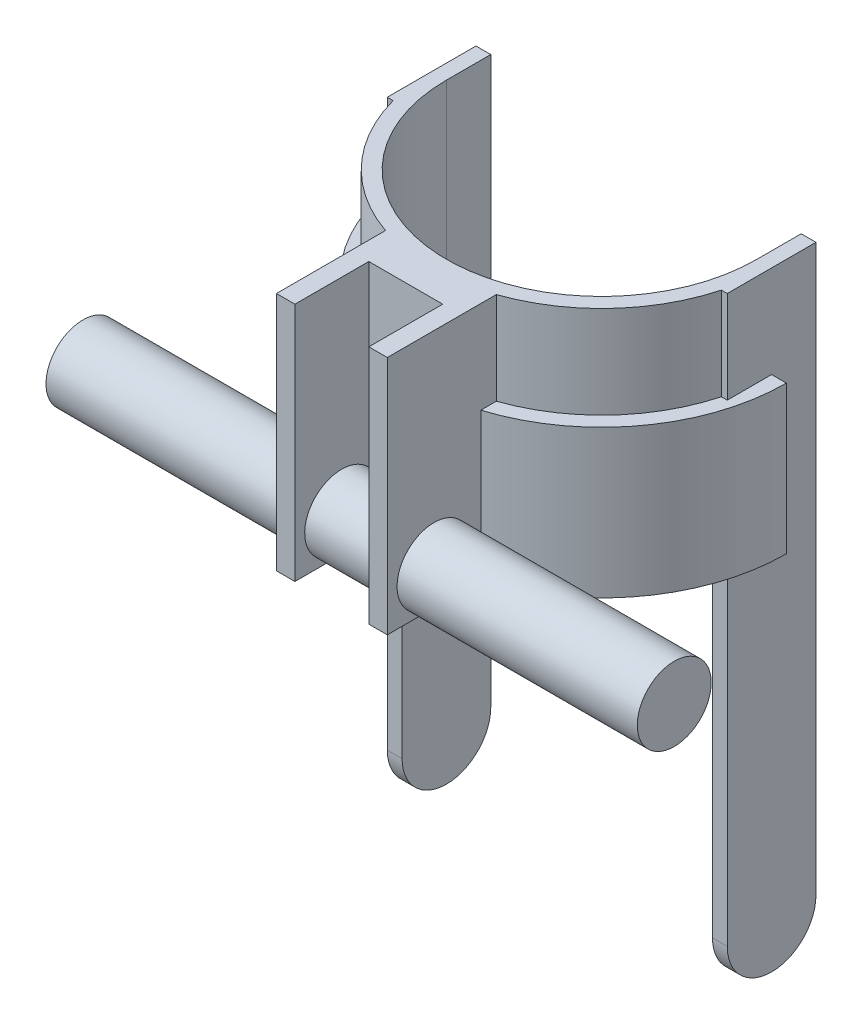
SolidWorks part; units mm, degrees
ref_plane "Front" through (0, 0, 0) normal (0, 0, 1) x (1, 0, 0)
ref_plane "Top" through (0, 0, 0) normal (0, 1, 0) x (1, 0, 0)
ref_plane "Right" through (0, 0, 0) normal (1, 0, 0) x (0, 0, -1)
sketch "草图1" plane through (0, 0, 0) normal (0, 1, 0) x (1, 0, 0)
  line L0 (-42, 0) -> (0, 0) construction
  line L1 (-46, 0) -> (-84.254, 0) construction
  line L2 (0, 0) -> (0, 41.4) construction
  line L5 (-46, 0) -> (-46, 12)
  line L6 (-46, 12) -> (-42, 12)
  line L7 (-42, 0) -> (-42, 12)
  line L11 (46, 0) -> (46, 12)
  line L12 (46, 12) -> (42, 12)
  line L13 (42, 0) -> (42, 12)
  line L14 (0, -42) -> (43.7489, -42) construction
  line L16 (-15, -43.4856) -> (-15, -73)
  line L17 (-15, -73) -> (-10, -73)
  line L18 (15, -43.4856) -> (15, -73)
  line L19 (10, -73) -> (15, -73)
  line L21 (-10, -73) -> (-10, -53)
  line L22 (-10, -53) -> (10, -53)
  line L23 (10, -73) -> (10, -53)
  arc A2 (-46, 0) -> (-15, -43.4856) centre (0, 0) ccw
  arc A3 (-42, 0) -> (42, 0) centre (0, 0) ccw
  arc A4 (15, -43.4856) -> (46, 0) centre (0, 0) ccw
  dimension "D1" = 12
  dimension "D2" = 12
  dimension "D3" = 30
  dimension "D4" = 15
  dimension "D7" = 10
  dimension "D8" = 20
  dimension "D9" = 20
extrude "凸台-拉伸1" add sketch "草图1" along normal mid plane 100
sketch "草图2" plane through (0, 50, 0) normal (0, 1, 0) x (1, 0, 0)
  line L9 (-46, 12) -> (-42, 12)
  line L10 (-46, 12) -> (-46, -12)
  line L11 (-46, -12) -> (-42, -12)
  line L12 (-42, 12) -> (-42, -12)
  line L13 (46, 12) -> (42, 12)
  line L14 (46, 12) -> (46, -12)
  line L15 (46, -12) -> (42, -12)
  line L16 (42, 12) -> (42, -12)
  dimension "D1" = 24
  dimension "D2" = 4
  dimension "D3" = 4
  dimension "D4" = 24
extrude "凸台-拉伸2" add sketch "草图2" against normal blind 210
sketch "草图3" plane through (46, 0, 0) normal (1, 0, 0) x (0, 0, -1)
  line L6 (-12, -138) -> (-12, -169.3796)
  line L7 (-12, -169.3796) -> (12, -169.3796)
  line L8 (12, -138) -> (12, -169.3796)
  arc A1 (-12, -138) -> (12, -138) centre (0, -138) ccw
extrude "切除-拉伸1" cut sketch "草图3" against normal through all
sketch "草图4" plane through (0, 50, 0) normal (0, 1, 0) x (1, 0, 0)
  line L1 (46, 12) -> (42, 12)
  line L2 (46, 12) -> (46, -12)
  line L3 (46, -12) -> (42, -12)
  line L4 (42, 12) -> (42, -12)
  line L5 (-46, 12) -> (-42, 12)
  line L6 (-46, 12) -> (-46, -12)
  line L7 (-46, -12) -> (-42, -12)
  line L8 (-42, 12) -> (-42, -12)
  dimension "D1" = 4
  dimension "D2" = 24
  dimension "D3" = 4
  dimension "D4" = 24
extrude "凸台-拉伸3" add sketch "草图4" along normal blind 260
sketch "草图5" plane through (0, 310, 0) normal (0, 1, 0) x (1, 0, 0)
  line L0 (965.5016, 12) -> (42, 12) construction
  line L1 (-48.5386, 12) -> (-42, 12)
  line L2 (42, 12) -> (48.5386, 12)
  line L3 (-42, 12) -> (-42, 0)
  line L4 (-42, 12) -> (-56.8817, 12) construction
  line L5 (42, 12) -> (42, 0)
  line L6 (40.2492, 12) -> (-40.2492, 12) construction
  arc A0 (-42, 0) -> (42, 0) centre (0, 0) ccw
  arc A1 (-48.5386, 12) -> (48.5386, 12) centre (0, 0) ccw
extrude "凸台-拉伸4" add sketch "草图5" against normal blind 30
sketch "草图6" plane through (46, 0, 0) normal (1, 0, 0) x (0, 0, -1)
  line L0 (0, 280) -> (0, 132.2251) construction
  line L1 (-12, 280) -> (12, 280) construction
  line L2 (-12, 280) -> (12, 280) construction
  line L3 (12, 280) -> (12, -138) construction
  circle A0 centre (0, 200) radius 4
  dimension "D1" = 80
extrude "切除-拉伸2" cut sketch "草图6" against normal through all
sketch "草图8" plane through (0, 0, -12) normal (0, 0, -1) x (-1, 0, 0)
  line L1 (-70.7811, 318.0863) -> (92.1217, 318.0863)
  line L2 (-70.7811, 318.0863) -> (-70.7811, 15)
  line L3 (-70.7811, 15) -> (92.1217, 15)
  line L4 (92.1217, 318.0863) -> (92.1217, 15)
  dimension "D1" = 15
extrude "切除-拉伸4" cut sketch "草图8" against normal through all
sketch "草图9" plane through (0, -50, 0) normal (0, -1, 0) x (1, 0, 0)
  line L0 (-50, 0) -> (-46, 0) construction
  line L1 (-50, 0) -> (-46, 0)
  line L2 (46, 0) -> (50, 0) construction
  line L3 (46, 0) -> (50, 0)
  arc A0 (46, 0) -> (-46, 0) centre (0, 0) ccw
  arc A1 (50, 0) -> (-50, 0) centre (0, 0) ccw
extrude "凸台-拉伸5" add sketch "草图9" against normal blind 40
sketch "草图10" plane through (0, 0, 0) normal (1, 0, 0) x (0, 0, -1)
  line L0 (-60.3485, -50) -> (-60.3485, 21.8958) construction
  line L1 (-73, -50) -> (-47.697, -50) construction
  circle A0 centre (-60.3485, -40) radius 10
extrude "凸台-拉伸6" add sketch "草图10" along normal mid plane 160
